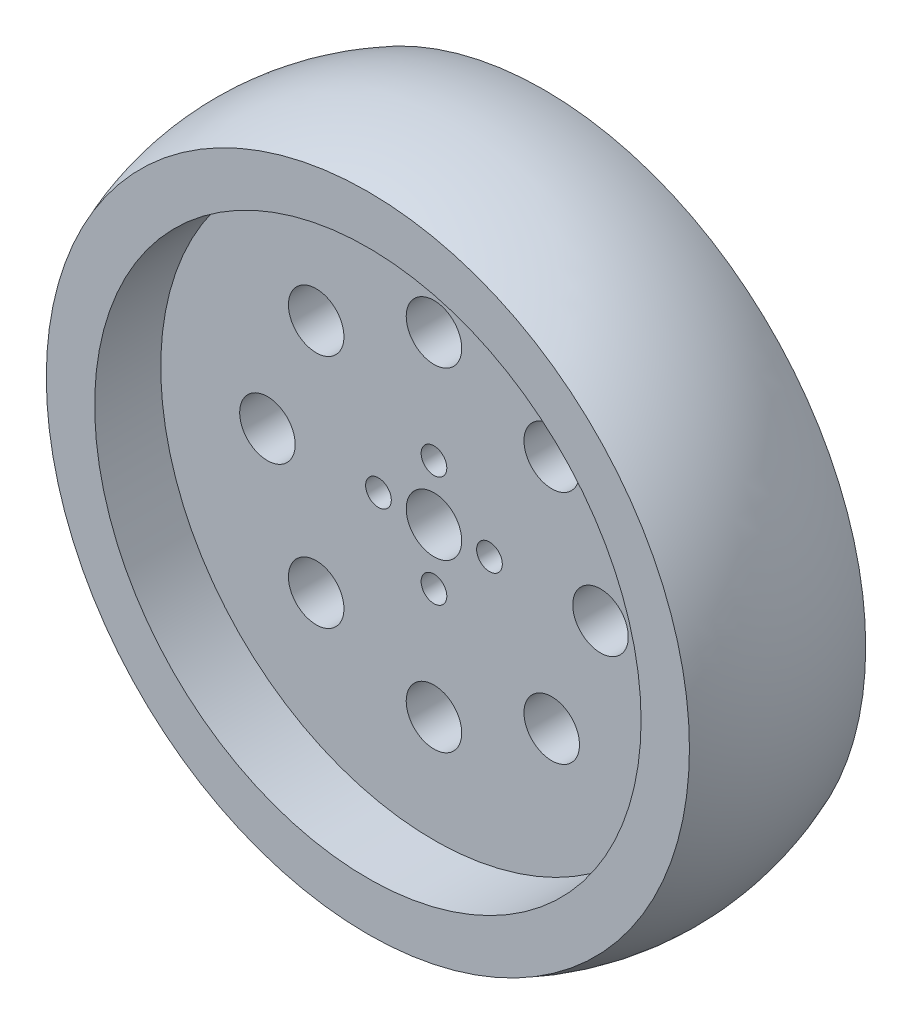
SolidWorks part; units mm, degrees
material "PE High Density"
ref_plane "Front Plane" through (0, 0, 0) normal (0, 0, 1) x (1, 0, 0)
ref_plane "Top Plane" through (0, 0, 0) normal (0, 1, 0) x (1, 0, 0)
ref_plane "Right Plane" through (0, 0, 0) normal (1, 0, 0) x (0, 0, -1)
sketch "Sketch1" plane through (0, 0, 0) normal (0, 1, 0) x (1, 0, 0)
  line L0 (46.339, 12.7) -> (0, 12.7)
  line L1 (0, 12.7) -> (0, -12.7)
  line L2 (0, -12.7) -> (46.339, -12.7)
  line L3 (0, 12.7) -> (0, -12.7) construction
  arc A0 (46.339, -12.7) -> (46.339, 12.7) centre (14.8, 0) ccw
revolve "Revolve1" add sketch "Sketch1" angle 360 about L3
sketch "Sketch2" plane through (0, 0, 0) normal (0, 1, 0) x (1, 0, 0)
  line L0 (39.37, 12.7) -> (0, 12.7)
  line L1 (0, 12.7) -> (0, -12.7)
  line L2 (0, -12.7) -> (39.37, -12.7)
  line L3 (39.37, -12.7) -> (39.37, -3.175)
  line L4 (39.37, -3.175) -> (4, -3.175)
  line L5 (4, -3.175) -> (4, 3.175)
  line L6 (4, 3.175) -> (39.37, 3.175)
  line L7 (39.37, 3.175) -> (39.37, 12.7)
  line L8 (0, 12.7) -> (0, -12.7) construction
revolve "Cut-Revolve1" cut sketch "Sketch2" angle 360 about L8
hole_wizard "Ø8.0 (8) Diameter Hole1" positions "Sketch4" profile "Sketch3" hole size "Ø8.0" standard "ANSI Metric"
sketch "Sketch4" plane through (0, 0, -3.175) normal (0, 0, -1) x (-1, 0, 0)
  point P0 (0, -24)
  point P1 (-16.9706, -16.9706)
  point P2 (-24, 0)
  point P3 (-16.9706, 16.9706)
  point P4 (0, 24)
  point P5 (16.9706, 16.9706)
  point P6 (24, 0)
  point P7 (16.9706, -16.9706)
sketch "Sketch3" plane through (0, -24, -3.175) normal (1, 0, 0) x (0, 1, 0)
  line L0 (0, 0) -> (0, 15.875)
  line L1 (0, 15.875) -> (4, 15.875)
  line L2 (4, 15.875) -> (4, 0)
  line L5 (4, 0) -> (0, 0)
  line L11 (0, -6.35) -> (0, 107.95) construction
  dimension "Thru Hole Dia." = 8
  dimension "Thru Hole Depth" = 15.875
hole_wizard "Ø3.7 (3.7) Diameter Hole1" positions "Sketch6" profile "Sketch5" hole size "Ø3.7" standard "ANSI Metric"
sketch "Sketch6" plane through (0, 0, -3.175) normal (0, 0, -1) x (-1, 0, 0)
  point P0 (-8, 0)
  point P1 (0, -8)
  point P2 (8, 0)
  point P3 (0, 8)
sketch "Sketch5" plane through (8, 0, -3.175) normal (1, 0, 0) x (0, 1, 0)
  line L0 (0, 0) -> (0, 15.875)
  line L1 (0, 15.875) -> (1.85, 15.875)
  line L2 (1.85, 15.875) -> (1.85, 0)
  line L5 (1.85, 0) -> (0, 0)
  line L11 (0, -6.35) -> (0, 107.95) construction
  dimension "Thru Hole Dia." = 3.7
  dimension "Thru Hole Depth" = 15.875
